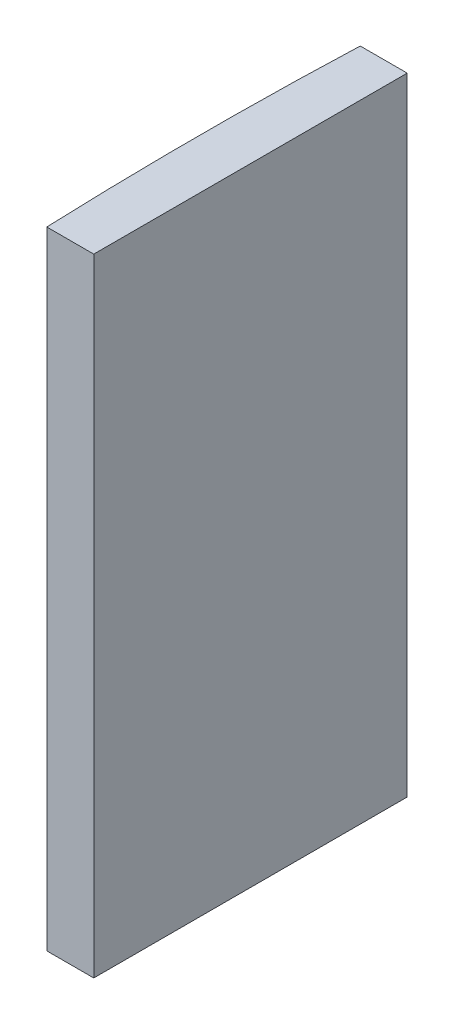
SolidWorks part; units mm, degrees
ref_plane "前视基准面" through (0, 0, 0) normal (0, 0, 1) x (1, 0, 0)
ref_plane "上视基准面" through (0, 0, 0) normal (0, 1, 0) x (1, 0, 0)
ref_plane "右视基准面" through (0, 0, 0) normal (1, 0, 0) x (0, 0, -1)
sketch "草图1" plane through (0, 0, 0) normal (0, 1, 0) x (1, 0, 0)
  line L0 (10.7432, 0) -> (-607.0701, 0) construction
  line L1 (-253.9513, 10) -> (-250.9548, 10)
  line L2 (-253.9513, -10) -> (-250.9548, -10)
  line L3 (-250.9548, 10) -> (-250.9548, -10)
  arc A0 (-253.9513, 10) -> (-253.9513, -10) centre (4.3552, 0) ccw
  point P19 (-254.1448, 0)
  point P20 (-250.9548, 0)
  dimension "D2" = 10
  dimension "D3" = 258.5
  dimension "D4" = 3.19
  dimension "D1" = 10
extrude "凸台-拉伸1" add sketch "草图1" along normal blind 40
